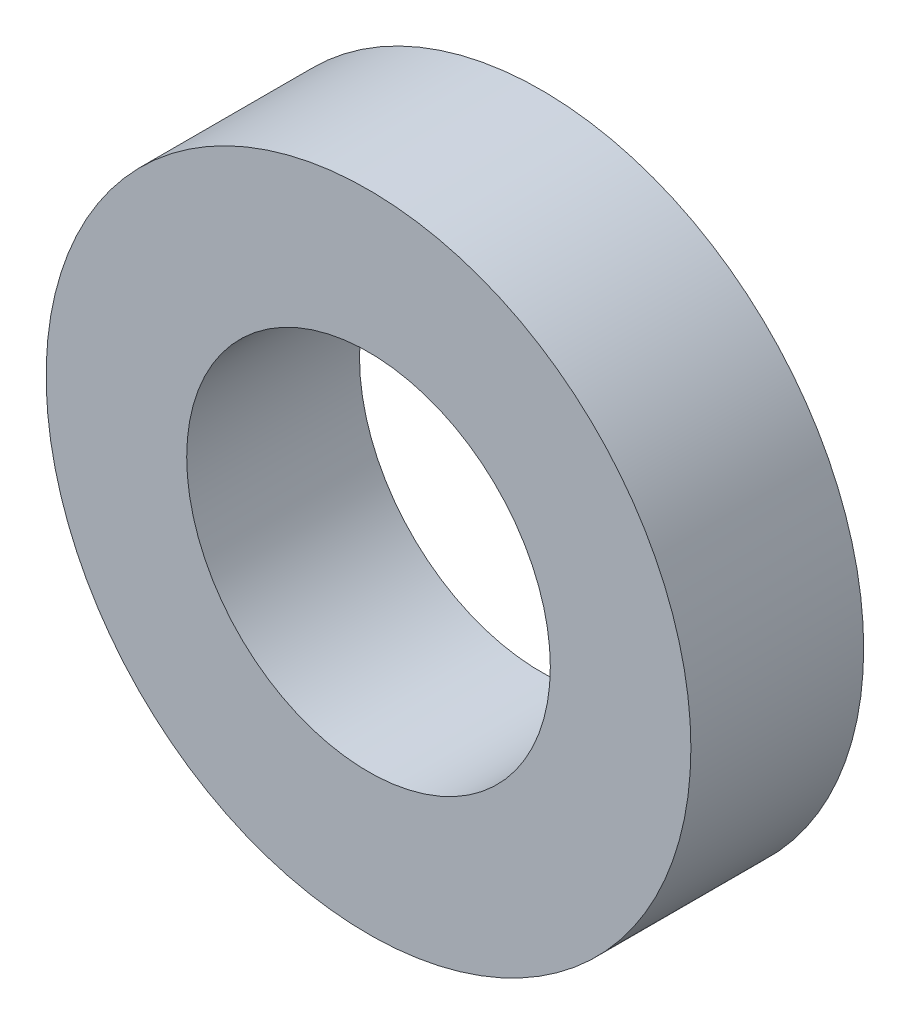
SolidWorks part; units mm, degrees
material "POLYURETHANE (11671)"
ref_plane "Front Plane" through (0, 0, 0) normal (0, 0, 1) x (1, 0, 0)
ref_plane "Top Plane" through (0, 0, 0) normal (0, 1, 0) x (1, 0, 0)
ref_plane "Right Plane" through (0, 0, 0) normal (1, 0, 0) x (0, 0, -1)
sketch "Sketch1" plane through (0, 0, 0) normal (0, 0, 1) x (1, 0, 0)
  circle A0 centre (0, 0) radius 1.7907
  circle A1 centre (0, 0) radius 3.175
  dimension "ID" = 3.5814
  dimension "OD" = 6.35
extrude "Extrude1" add sketch "Sketch1" against normal blind 1.7018
